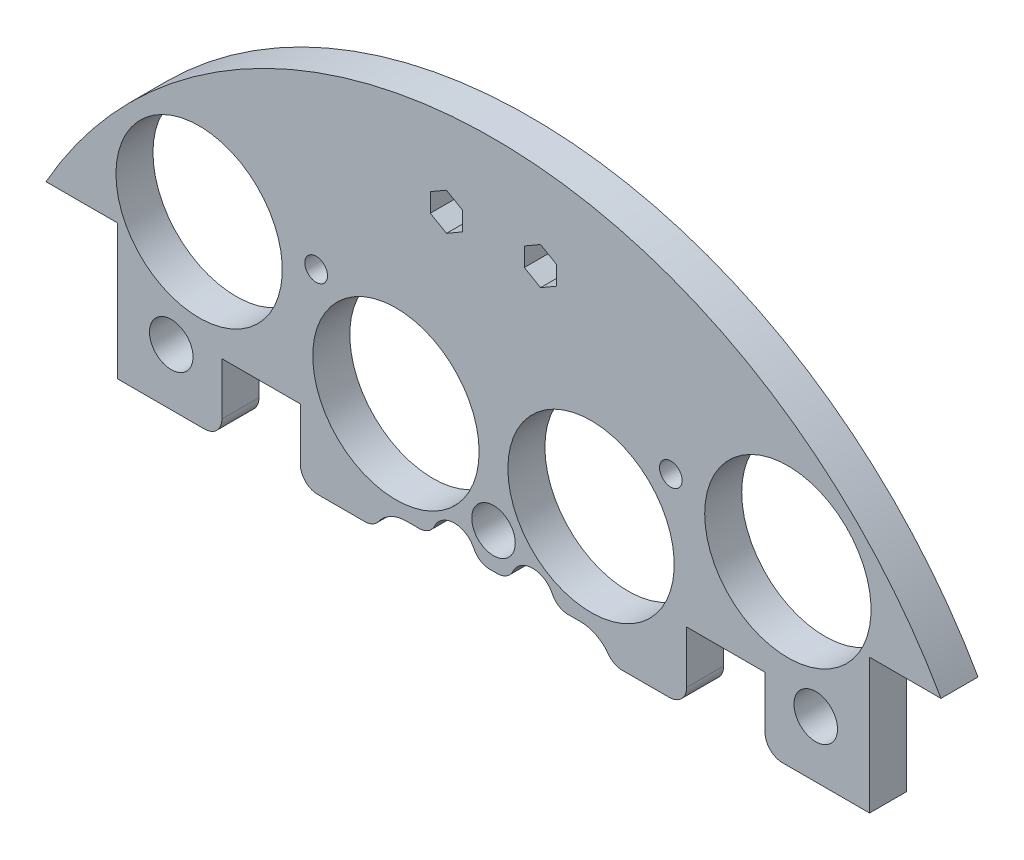
SolidWorks part; units mm, degrees
ref_plane "Front Plane" through (0, 0, 0) normal (0, 0, 1) x (1, 0, 0)
ref_plane "Top Plane" through (0, 0, 0) normal (0, 1, 0) x (1, 0, 0)
ref_plane "Right Plane" through (0, 0, 0) normal (1, 0, 0) x (0, 0, -1)
sketch "Sketch1" plane through (0, 0, 0) normal (0, 0, 1) x (1, 0, 0)
  line L0 (0, 0) -> (-82.1241, 0) construction
  line L1 (0, 0) -> (0, 95.6219) construction
  line L3 (-65.2538, 36.83) -> (-54.8398, 36.83)
  line L5 (-65.2538, -36.83) -> (-54.8398, -36.83)
  line L6 (-54.8398, 36.83) -> (-54.8398, -36.83)
  line L7 (65.2538, -36.83) -> (54.8398, -36.83)
  line L8 (65.2538, 36.83) -> (54.8398, 36.83)
  line L9 (54.8398, 36.83) -> (54.8398, -36.83)
  arc A0 (-65.2538, -36.83) -> (65.2538, -36.83) centre (0, 0) ccw
  circle A1 centre (-45.466, 11.049) radius 1.651
  circle A2 centre (-20.0673, 10.795) radius 1.651
  circle A3 centre (-20.0673, -10.795) radius 1.651
  circle A4 centre (-45.466, -11.049) radius 1.651
  circle A5 centre (45.466, -11.049) radius 1.651
  circle A6 centre (20.0673, -10.795) radius 1.651
  circle A7 centre (20.0673, 10.795) radius 1.651
  circle A8 centre (45.466, 11.049) radius 1.651
  arc A9 (65.2538, 36.83) -> (-65.2538, 36.83) centre (0, 0) ccw
  dimension "D2" = 3.302
  dimension "D3" = 3.302
  dimension "D4" = 25.4
  dimension "D5" = 10.795
  dimension "D10" = 45.466
  dimension "D6" = 73.66
  dimension "D7" = 10.414
  dimension "D8" = 74.93
  dimension "D9" = 74.93
  dimension "D11" = 36.83
extrude "Boss-Extrude2" add sketch "Sketch1" along normal blind 5.3975
sketch "Sketch2" plane through (0, 0, 5.3975) normal (0, 0, 1) x (1, 0, 0)
  line L0 (0, 68.58) -> (0, 55.88) construction
  line L1 (-9.525, 68.58) -> (9.525, 68.58)
  line L2 (-9.525, 68.58) -> (-9.525, 55.88)
  line L3 (-9.525, 55.88) -> (9.525, 55.88)
  line L4 (9.525, 68.58) -> (9.525, 55.88)
  line L5 (-9.525, 62.23) -> (9.525, 62.23) construction
  arc A0 (65.2538, 36.83) -> (-65.2538, 36.83) centre (0, 0) ccw construction
  circle A1 centre (-20.0673, 10.795) radius 1.651 construction
  circle A2 centre (20.0673, 10.795) radius 1.651 construction
  circle A3 centre (-6.731, 62.23) radius 1.143
  circle A4 centre (6.731, 62.23) radius 1.143
  dimension "D4" = 2.286
  dimension "D5" = 0
  dimension "D6" = 6.731
  dimension "D1" = 19.05
  dimension "D2" = 12.7
  dimension "D3" = 55.88
extrude "Cut-Extrude1" cut sketch "Sketch2" against normal through all contours A3 | A4
sketch "Sketch3" plane through (0, 0, 0) normal (0, 0, -1) x (-1, 0, 0)
  line L0 (0, 0) -> (0, -116.2908) construction
  line L1 (0, 0) -> (-153.8039, 0) construction
  arc A1 (65.2538, 36.83) -> (-65.2538, 36.83) centre (0, 0) ccw construction
  circle A4 centre (-42.926, -42.926) radius 12.1285
  circle A6 centre (14.224, -34.29) radius 12.1285
  circle A7 centre (14.224, 34.29) radius 12.1285
  circle A8 centre (-42.926, 42.926) radius 12.1285
  circle A11 centre (42.926, 42.926) radius 12.1285
  circle A12 centre (-14.224, 34.29) radius 12.1285
  circle A13 centre (-14.224, -34.29) radius 12.1285
  circle A14 centre (42.926, -42.926) radius 12.1285
  point P36 (0, 0)
  point P53 (0, 0)
  point P55 (0, 0)
  dimension "D1" = 34.29
  dimension "D2" = 14.224
  dimension "D3" = 42.926
  dimension "D4" = 24.257
  dimension "D5" = 42.926
  dimension "D6" = 42.926
extrude "Cut-Extrude2" cut sketch "Sketch3" against normal through all
sketch "Sketch4" plane through (0, 0, 0) normal (0, 0, -1) x (-1, 0, 0)
  line L1 (-15.7702, 56.3138) -> (12.7925, 56.3138)
  line L2 (-15.7702, 56.3138) -> (-15.7702, 67.9913)
  line L3 (-15.7702, 67.9913) -> (12.7925, 67.9913)
  line L4 (12.7925, 56.3138) -> (12.7925, 67.9913)
extrude "Boss-Extrude3" add sketch "Sketch4" against normal up to surface (5.3975 mm away) up to face at (-55.0545, -42.926, 5.3975)
sketch "Sketch5" plane through (0, 0, 0) normal (0, 0, -1) x (-1, 0, 0)
  line L1 (-113.3786, -90.442) -> (117.3207, -90.442)
  line L2 (-113.3786, -90.442) -> (-113.3786, 17.145)
  line L3 (-113.3786, 17.145) -> (117.3207, 17.145)
  line L4 (117.3207, -90.442) -> (117.3207, 17.145)
  circle A1 centre (20.0673, 10.795) radius 1.651 construction
  dimension "D1" = 6.35
extrude "Cut-Extrude3" cut sketch "Sketch5" against normal through all
sketch "Sketch6" plane through (0, 0, 0) normal (0, 0, -1) x (-1, 0, 0)
  line L0 (0, 0) -> (0, 114.5161) construction
  line L1 (4.498, 63.5925) -> (6.858, 64.9551)
  line L2 (-6.858, 64.9551) -> (-9.218, 63.5925)
  line L3 (-9.218, 63.5925) -> (-9.218, 60.8675)
  line L4 (-9.218, 60.8675) -> (-6.858, 59.5049)
  line L5 (-6.858, 59.5049) -> (-4.498, 60.8675)
  line L6 (-4.498, 60.8675) -> (-4.498, 63.5925)
  line L7 (-4.498, 63.5925) -> (-6.858, 64.9551)
  line L8 (4.498, 60.8675) -> (4.498, 63.5925)
  line L9 (6.858, 59.5049) -> (4.498, 60.8675)
  line L10 (9.218, 60.8675) -> (6.858, 59.5049)
  line L11 (9.218, 63.5925) -> (9.218, 60.8675)
  line L12 (6.858, 64.9551) -> (9.218, 63.5925)
  circle A1 centre (6.858, 62.23) radius 2.36 construction
  circle A2 centre (-6.858, 62.23) radius 2.36 construction
  dimension "D2" = 6.858
  dimension "D4" = 4.72
  dimension "D3" = 62.23
extrude "Cut-Extrude4" cut sketch "Sketch6" against normal through all
extrude "Cut-Extrude55" cut sketch "Sketch57" against normal through all both and the other way through all
sketch "Sketch57" plane through (-29.8755, 133.1307, 31.75) normal (0, 0, 1) x (0.01, 0.9999, 0)
  line L0 (-132.614, -31.3134) -> (-132.614, 57.8454) construction
  line L1 (-132.614, -31.3134) -> (-222.516, -31.3134) construction
  circle A0 centre (-158.014, 14.4066) radius 3.175
  circle A1 centre (-173.254, -31.3134) radius 3.175
  circle A3 centre (-158.014, -77.0334) radius 3.175
  circle A4 centre (-107.214, -77.0334) radius 3.175
  circle A5 centre (-91.974, -31.3134) radius 3.175
  circle A6 centre (-107.214, 14.4066) radius 3.175
sketch "Sketch58" [suppressed] plane through (0, 0, 0) normal (0, 0, -1) x (-1, 0, 0)
  circle A0 centre (-46.082, 25.1518) radius 4.445
  circle A1 centre (-0.5167, 40.8482) radius 4.445
  circle A2 centre (45.3534, 26.0662) radius 4.445
  circle A3 centre (-46.082, 25.1518) radius 3.175 construction
  circle A4 centre (-0.5167, 40.8482) radius 3.175 construction
  circle A5 centre (45.3534, 26.0662) radius 3.175 construction
  dimension "D1" = 1.27
  dimension "D2" = 1.27
  dimension "D3" = 1.27
extrude "Boss-Extrude4" [suppressed] add sketch "Sketch58" against normal up to surface (6.35 mm away)
extrude "Cut-Extrude56" cut sketch "Sketch59" against normal through all both and the other way through all
sketch "Sketch59" plane through (31.3134, 132.614, -19.05) normal (0, 0, -1) x (0, 1, 0)
  line L0 (-132.614, -31.3134) -> (-132.614, 57.8454) construction
  line L1 (-132.614, -31.3134) -> (-222.516, -31.3134) construction
  circle A0 centre (-158.014, 14.4066) radius 3.175
  circle A1 centre (-173.254, -31.3134) radius 3.175
  circle A3 centre (-158.014, -77.0334) radius 3.175
  circle A4 centre (-107.214, -77.0334) radius 3.175
  circle A5 centre (-91.974, -31.3134) radius 3.175
  circle A6 centre (-107.214, 14.4066) radius 3.175
extrude "Cut-Extrude60" cut sketch "Sketch63" against normal blind 29.21
sketch "Sketch63" plane through (31.3134, 132.559, -15.875) normal (0, 0, -1) x (0, 1, 0)
  line L0 (-132.559, -31.3134) -> (6.1626, -31.3134) construction
  line L2 (-132.559, -31.3134) -> (-132.559, -122.6589) construction
  circle A0 centre (-190.979, 2.9766) radius 1.651
  circle A2 centre (-154.784, -31.3134) radius 1.651
  circle A3 centre (-190.979, -65.6034) radius 1.651
  circle A4 centre (-110.334, -31.3134) radius 1.651
  circle A5 centre (-74.139, -65.6034) radius 1.651
  circle A6 centre (-74.139, 2.9766) radius 1.651
extrude "Cut-Extrude151" cut sketch "Sketch155" against normal blind 29.21
sketch "Sketch155" plane through (-31.3134, 132.559, 15.875) normal (0, 0, 1) x (0, 1, 0)
  line L0 (-143.7712, -34.3645) -> (6.1626, -34.3645) construction
  line L2 (-143.7712, -34.3645) -> (-143.7712, -122.6589) construction
  circle A0 centre (-202.1912, -0.0745) radius 1.651
  circle A2 centre (-165.9962, -34.3645) radius 1.651
  circle A3 centre (-202.1912, -68.6545) radius 1.651
  circle A4 centre (-121.5462, -34.3645) radius 1.651
  circle A5 centre (-85.3512, -68.6545) radius 1.651
  circle A6 centre (-85.3512, -0.0745) radius 1.651
sketch "Sketch156" plane through (0, 0, 0) normal (0, 0, -1) x (-1, 0, 0)
  line L0 (54.8398, 17.145) -> (-54.8398, 17.145) construction
  line L1 (39.5998, 17.145) -> (28.1698, 17.145)
  line L2 (39.5998, 17.145) -> (39.5998, 27.305)
  line L3 (39.5998, 27.305) -> (28.1698, 27.305)
  line L4 (28.1698, 17.145) -> (28.1698, 27.305)
  line L5 (54.8398, 36.83) -> (54.8398, 17.145) construction
  line L6 (-28.1698, 17.145) -> (-39.5998, 17.145)
  line L7 (-28.1698, 17.145) -> (-28.1698, 27.305)
  line L8 (-28.1698, 27.305) -> (-39.5998, 27.305)
  line L9 (-39.5998, 17.145) -> (-39.5998, 27.305)
  line L10 (0, 8.076) -> (0, 81.5725) construction
  dimension "D1" = 10.16
  dimension "D2" = 11.43
  dimension "D3" = 15.24
extrude "Cut-Extrude152" cut sketch "Sketch156" against normal through all
sketch "Sketch164" plane through (0, 0, 0) normal (0, 0, -1) x (-1, 0, 0)
  line L0 (0, 0) -> (0, 91.2301) construction
  circle A0 centre (25.8572, 45.466) radius 1.651
  circle A1 centre (42.926, 42.926) radius 12.1285 construction
  circle A2 centre (14.224, 34.29) radius 12.1285 construction
  circle A3 centre (-25.8572, 45.466) radius 1.651
  dimension "D1" = 3.302
  dimension "D2" = 2.54
  dimension "D3" = 11.6332
extrude "Cut-Extrude160" cut sketch "Sketch164" against normal blind 21.59
extrude "Cut-Extrude214" cut sketch "Sketch218" against normal blind 48.768 and the other way blind 103.378
sketch "Sketch218" plane through (30.092, 4.0835, 11.4935) normal (0, 0, -1) x (-1, 0, 0)
  line L0 (30.092, -4.0835) -> (148.6336, -4.0835) construction
  line L1 (30.092, -4.0835) -> (30.092, 90.452) construction
  circle A0 centre (-16.898, 21.3165) radius 3.175
  circle A1 centre (77.082, 21.3165) radius 3.175
  circle A2 centre (30.092, 21.3165) radius 3.175
  circle A4 centre (77.082, -29.4835) radius 3.175
  circle A5 centre (30.092, -29.4835) radius 3.175
  circle A6 centre (-16.898, -29.4835) radius 3.175
sketch "Sketch159" plane through (0, 0, 0) normal (0, 0, -1) x (-1, 0, 0)
  line L0 (0, 0) -> (0, 10.24) construction
  line L1 (-12.7, 20.24) -> (-8.889, 20.24)
  line L2 (-12.7, 10.24) -> (12.7, 10.24)
  line L3 (0, 20.24) -> (0, 25.4) construction
  line L4 (8.889, 20.24) -> (12.7, 20.24)
  line L5 (-2.541, 20.24) -> (2.541, 20.24)
  arc A0 (12.7, 10.24) -> (12.7, 20.24) centre (12.7, 15.24) ccw
  arc A1 (-12.7, 10.24) -> (-12.7, 20.24) centre (-12.7, 15.24) cw
  arc A2 (-2.541, 20.24) -> (-8.889, 20.24) centre (-5.715, 20.32) ccw
  arc A3 (8.889, 20.24) -> (2.541, 20.24) centre (5.715, 20.32) ccw
  dimension "D1" = 10
  dimension "D4" = 6.35
  dimension "D5" = 6.35
  dimension "D2" = 15.24
  dimension "D3" = 12.7
  dimension "D6" = 11.43
  dimension "D7" = 5.715
  dimension "D8" = 20.32
extrude "Cut-Extrude155" cut sketch "Sketch159" against normal blind 34.544
fillet "Fillet1" radius 2.54 10 edges at (39.5998, 17.145, 2.6987) (28.1698, 17.145, 2.6987) (17.3229, 17.145, 2.6987) (8.889, 20.24, 2.6987) (2.541, 20.24, 2.6987) (-2.541, 20.24, 2.6987) (-8.889, 20.24, 2.6987) (-17.3229, 17.145, 2.6987) (-28.1698, 17.145, 2.6987) (-39.5998, 17.145, 2.6987)
